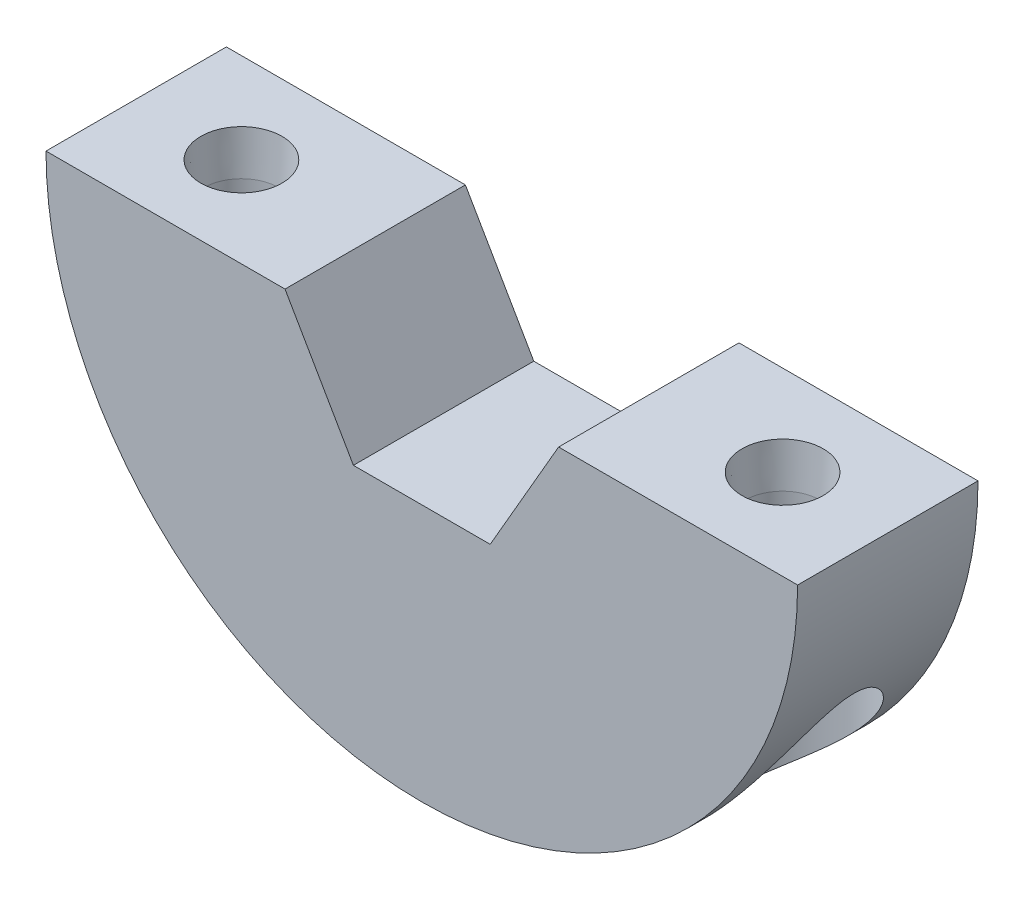
SolidWorks part; units mm, degrees
ref_plane "Front Plane" through (0, 0, 0) normal (0, 0, 1) x (1, 0, 0)
ref_plane "Top Plane" through (0, 0, 0) normal (0, 1, 0) x (1, 0, 0)
ref_plane "Right Plane" through (0, 0, 0) normal (1, 0, 0) x (0, 0, -1)
sketch "Sketch1" plane through (0, 0, 0) normal (0, 0, 1) x (1, 0, 0)
  line L0 (-25, 0) -> (-9.1, 0)
  line L1 (9.1, 0) -> (25, 0)
  line L11 (-9.1, 0) -> (9.2113, 0)
  line L12 (-25, 0) -> (25, 0)
  arc A0 (-25, 0) -> (25, 0) centre (0, 0) ccw
  dimension "D1" = 25
extrude "Boss-Extrude1" add sketch "Sketch1" along normal blind 12 contours L0 A0 L1 L11
ref_plane "Plane1" through (0, -40, 0) normal (0, 1, 0) x (1, 0, 0)
sketch "Sketch2" plane through (0, -40, 0) normal (0, 1, 0) x (1, 0, 0)
  line L1 (-25, -12) -> (25, -12) construction
  circle A0 centre (-18, -6) radius 4.75
  circle A1 centre (18, -6) radius 4.75
  dimension "D1" = 9.5
  dimension "D2" = 9.5
  dimension "D3" = 6
  dimension "D4" = 6
  dimension "D5" = 18
  dimension "D6" = 18
extrude "Cut-Extrude1" cut sketch "Sketch2" along normal blind 35 contours A1 | A0
sketch "Sketch3" plane through (0, -5, 0) normal (0, -1, 0) x (1, 0, 0)
  circle A0 centre (18, 6) radius 2.05
  circle A1 centre (-18, 6) radius 2.05
  dimension "D1" = 4.1
  dimension "D2" = 4.1
extrude "Cut-Extrude2" cut sketch "Sketch3" against normal blind 35
sketch "Sketch4" plane through (0, 0, 12) normal (0, 0, 1) x (1, 0, 0)
  line L0 (-25, 0) -> (25, 0) construction
  line L1 (9.1, 0) -> (4.55, 7.8808)
  line L2 (4.55, 7.8808) -> (-4.55, 7.8808)
  line L3 (-4.55, 7.8808) -> (-9.1, 0)
  line L4 (-9.1, 0) -> (-4.55, -7.8808)
  line L5 (-4.55, -7.8808) -> (4.55, -7.8808)
  line L6 (4.55, -7.8808) -> (9.1, 0)
  circle A0 centre (0, 0) radius 7.8808 construction
  dimension "D1" = 18.2
extrude "Cut-Extrude3" cut sketch "Sketch4" against normal blind 20
hole_wizard "CSK for M3 Cross Countersunk Head Screw1" positions "3DSketch1" profile "Sketch5" countersink size "M3" standard "AS" end condition through all
sketch3d "3DSketch1"
  line L0 (-18, 0, 6) -> (-18, -5, 6) construction
  line L1 (18, 0, 6) -> (18, -5, 6) construction
  point P0 (-18, 0, 6)
  point P4 (18, 0, 6)
sketch "Sketch5" plane through (-18, 0, 6) normal (1, 0, 0) x (0, 0, 1)
  line L0 (0, 0) -> (0, 25)
  line L1 (0, 25) -> (2.5, 25)
  line L2 (2.5, 25) -> (2.5, 2.8601)
  line L3 (2.5, 2.8601) -> (2.7, 0)
  line L5 (2.7, 0) -> (0, 0)
  line L6 (-2.5, 2.8601) -> (-2.7, 0) construction
  line L11 (0, -6.35) -> (0, 107.95) construction
  dimension "Thru Hole Dia." = 5
  dimension "Thru Hole Depth" = 25
  dimension "Near C'Sink Dia." = 5.4
  dimension "Near C'Sink Angle" = 8
